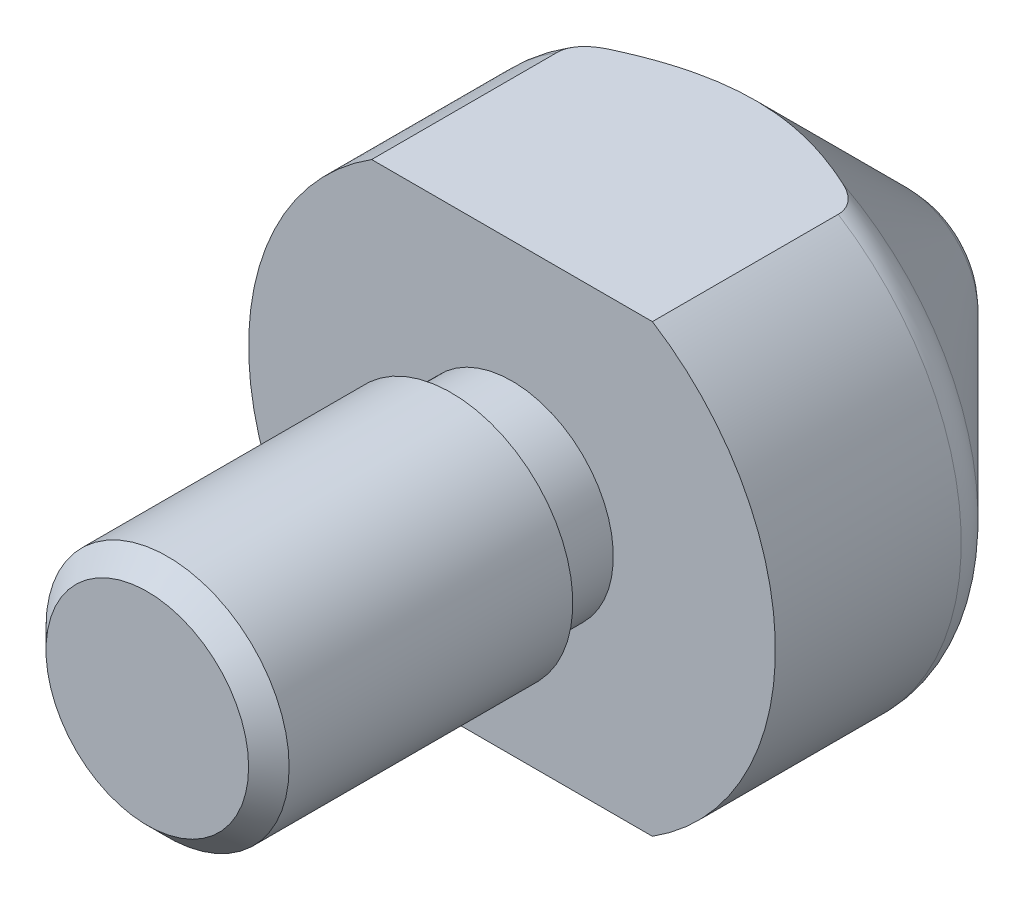
SolidWorks part; units mm, degrees
material "1.7225 (42CrMo4)"
ref_plane "Front Plane" through (0, 0, 0) normal (0, 0, 1) x (1, 0, 0)
ref_plane "Top Plane" through (0, 0, 0) normal (0, 1, 0) x (1, 0, 0)
ref_plane "Right Plane" through (0, 0, 0) normal (1, 0, 0) x (0, 0, -1)
sketch "Sketch1" plane through (0, 0, 0) normal (1, 0, 0) x (0, 0, -1)
  line L0 (1178.1082, 0) -> (978.3576, 0) construction
  line L1 (1009, 0) -> (1009, 6)
  line L2 (1009, 6) -> (1024, 6)
  line L3 (1024, 6) -> (1024, 5)
  line L4 (1024, 5) -> (1027, 5)
  line L5 (1027, -11.6688) -> (1027, 5.1948) construction
  line L6 (1027, 5) -> (1027, 13)
  line L7 (1027, -13) -> (1027, 13) construction
  line L8 (1027, 13) -> (1036.1716, 13)
  line L9 (1037.5858, 12.4142) -> (1046.4645, 3.5355)
  line L10 (1047.9289, 0) -> (1009, 0)
  arc A0 (1046.4645, 3.5355) -> (1047.9289, 0) centre (1042.9289, 0) cw
  arc A1 (1036.1716, 13) -> (1037.5858, 12.4142) centre (1036.1716, 11) cw
  point P20 (1037, 13)
  dimension "D4" = 5
  dimension "D9" = 2
  dimension "D1" = 26
  dimension "D2" = 10
  dimension "D3" = 45
  dimension "D5" = 12
  dimension "D6" = 10
  dimension "D7" = 3
  dimension "D8" = 18
revolve "Revolve1" add sketch "Sketch1" angle 360 about L0
sketch "Sketch2" plane through (0, 0, -1027) normal (0, 0, 1) x (1, 0, 0)
  line L1 (13, 11) -> (-13, 11)
  line L2 (13, 11) -> (13, -11)
  line L3 (13, -11) -> (-13, -11)
  line L4 (-13, 11) -> (-13, -11)
  line L5 (13, 11) -> (-13, -11) construction
  line L6 (13, -11) -> (-13, 11) construction
  circle A0 centre (0, 0) radius 13 construction
  point P0 (0, 0)
  dimension "D1" = 22
extrude "Cut-Extrude-Thin1" cut sketch "Sketch2" against normal through all thin
chamfer "Chamfer1" distance 1 angle 45 1 edges at (-6, 0, -1009)
